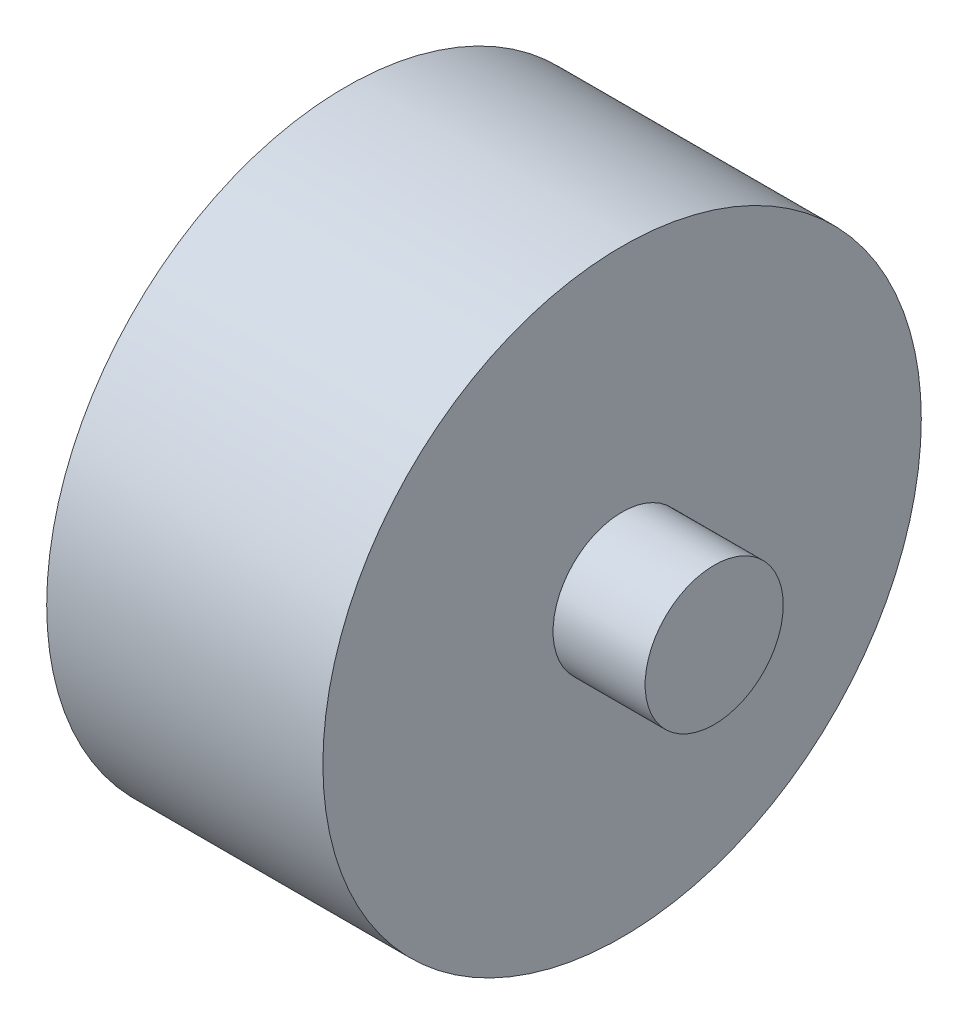
SolidWorks part; units mm, degrees
ref_plane "Front Plane" through (0, 0, 0) normal (0, 0, 1) x (1, 0, 0)
ref_plane "Top Plane" through (0, 0, 0) normal (0, 1, 0) x (1, 0, 0)
ref_plane "Right Plane" through (0, 0, 0) normal (1, 0, 0) x (0, 0, -1)
sketch "Sketch1" plane through (0, 0, 0) normal (1, 0, 0) x (0, 0, -1)
  circle A0 centre (0, 0) radius 65
  dimension "D1" = 130
extrude "Boss-Extrude1" add sketch "Sketch1" along normal blind 60
sketch "Sketch2" plane through (60, 0, 0) normal (1, 0, 0) x (0, 0, -1)
  circle A0 centre (0, 0) radius 15
  dimension "D1" = 30
extrude "Boss-Extrude2" add sketch "Sketch2" along normal blind 20
